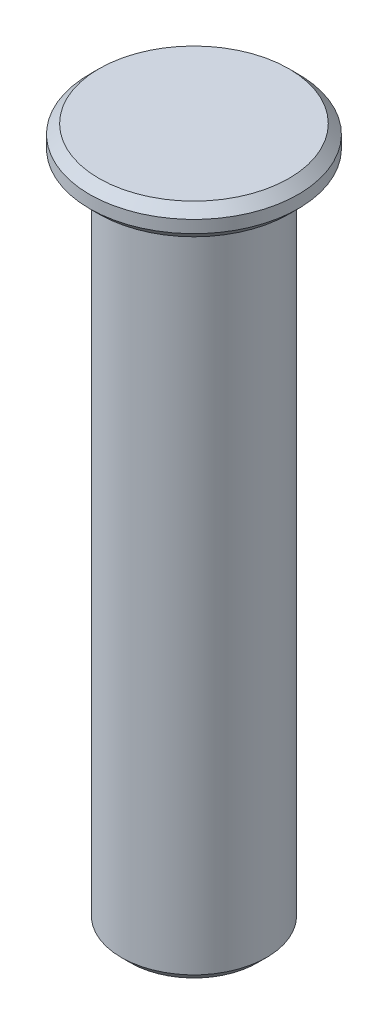
SolidWorks part; units mm, degrees
ref_plane "Front Plane" through (0, 0, 0) normal (0, 0, 1) x (1, 0, 0)
ref_plane "Top Plane" through (0, 0, 0) normal (0, 1, 0) x (1, 0, 0)
ref_plane "Right Plane" through (0, 0, 0) normal (1, 0, 0) x (0, 0, -1)
sketch "Sketch2" plane through (0, 0, 0) normal (0, 1, 0) x (1, 0, 0)
  circle A0 centre (0, 0) radius 4.7
  dimension "D1" = 9.4
extrude "Boss-Extrude1" add sketch "Sketch2" along normal blind 45
sketch "Sketch3" plane through (0, 45, 0) normal (0, 1, 0) x (1, 0, 0)
  circle A0 centre (0, 0) radius 6.75
  dimension "D1" = 13.5
extrude "Boss-Extrude2" add sketch "Sketch3" against normal blind 2
chamfer "Chamfer1" distance 0.6 angle 45 3 edges at (0, 0, 4.7) (0, 43, 6.75) (0, 45, 6.75)
